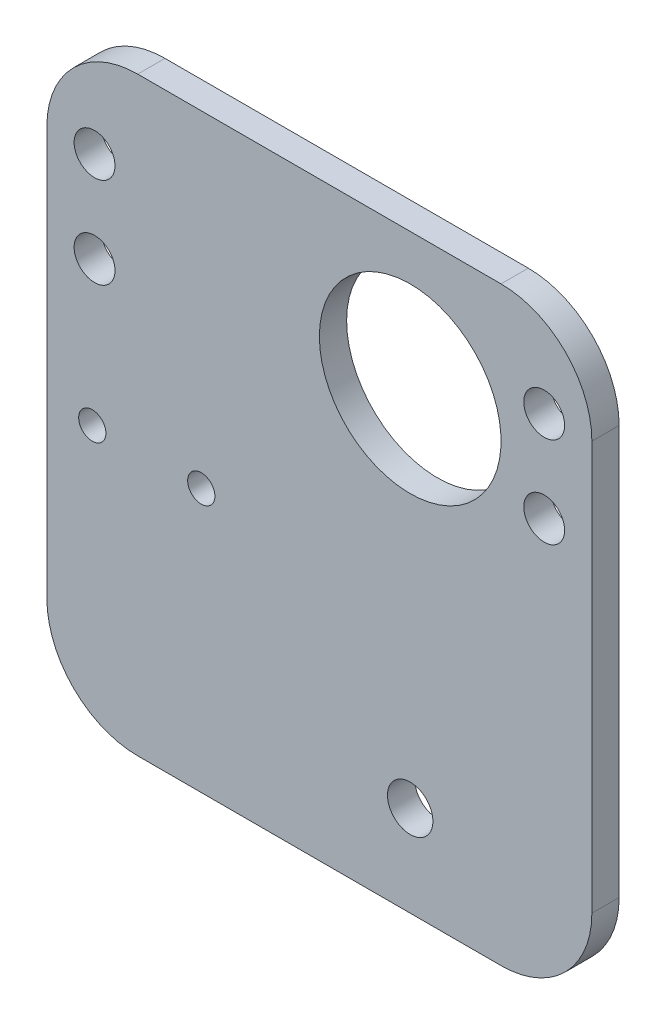
SolidWorks part; units mm, degrees
ref_plane "前视基准面" through (0, 0, 0) normal (0, 0, 1) x (1, 0, 0)
ref_plane "上视基准面" through (0, 0, 0) normal (0, 1, 0) x (1, 0, 0)
ref_plane "右视基准面" through (0, 0, 0) normal (1, 0, 0) x (0, 0, -1)
sketch "草图3" plane through (0, 0, 0) normal (0, 0, 1) x (1, 0, 0)
  line L0 (60.2665, 6.5325) -> (60.2665, 16.5325)
  line L1 (10.7665, 16.5325) -> (10.7665, 6.5325)
  line L2 (10.7665, 16.5325) -> (60.2665, 16.5325)
  circle A0 centre (60.2665, 16.5325) radius 3
  circle A1 centre (60.2665, 6.5325) radius 3
  circle A6 centre (10.7665, 6.5325) radius 3
  circle A7 centre (10.7665, 16.5325) radius 3
  dimension "D1" = 6
  dimension "D2" = 6
  dimension "D4" = 6
  dimension "D5" = 6
  dimension "D3" = 10
  dimension "D6" = 49.5
  dimension "D7" = 49.5
  dimension "D8" = 10
extrude "凸台-拉伸6" add sketch "草图3" along normal blind 0.001 contours A6 | A0 | A1 | A7
sketch "草图11" plane through (0, 0, 0.001) normal (0, 0, 1) x (1, 0, 0)
  circle A0 centre (10.7665, 16.5325) radius 2.25
  circle A1 centre (10.7665, 6.5325) radius 2.25
  circle A2 centre (60.2665, 16.5325) radius 2.25
  circle A3 centre (60.2665, 6.5325) radius 2.25
  dimension "D1" = 4.5
  dimension "D2" = 4.5
  dimension "D3" = 4.5
  dimension "D4" = 4.5
extrude "切除-拉伸2" cut sketch "草图11" against normal through all both and the other way through all
sketch "草图12" plane through (0, 0, 0.001) normal (0, 0, 1) x (1, 0, 0)
  line L4 (10.7665, 16.5325) -> (60.2665, 6.5325) construction
  line L5 (10.7665, 6.5325) -> (60.2665, 16.5325) construction
  line L6 (60.2665, 16.5325) -> (60.2665, 6.5325) construction
  line L7 (5.5165, 26.5325) -> (65.5165, 26.5325)
  line L8 (5.5165, 26.5325) -> (5.5165, 1.5325)
  line L9 (5.5165, -38.4675) -> (65.5165, -38.4675)
  line L10 (65.5165, 26.5325) -> (65.5165, -38.4675)
  line L11 (5.5165, 1.5325) -> (5.5165, -38.4675) construction
  line L13 (5.5165, -38.4675) -> (5.5165, 1.5325) construction
  line L16 (5.5165, 1.5325) -> (5.5165, -38.4675)
  circle A4 centre (45.5165, 11.5325) radius 10
  point P8 (35.5165, 11.5325)
  point P9 (35.5165, 26.5325)
  point P10 (-46.6091, 14.6442)
  point P11 (60.2665, 11.5325)
  dimension "D5" = 20
  dimension "D1" = 60
  dimension "D2" = 65
  dimension "D3" = 15
  dimension "D4" = 14.75
extrude "凸台-拉伸7" add sketch "草图12" along normal blind 3 contours L7 L10 L9 L16 L8
sketch "草图14" plane through (0, 0, 0.001) normal (0, 0, -1) x (-1, 0, 0)
  line L0 (-60.2665, 16.5325) -> (-60.2665, 6.5325) construction
  circle A0 centre (-60.2665, 6.5325) radius 2.25 construction
  circle A1 centre (-60.2665, 6.5325) radius 2.25
  circle A2 centre (-60.2665, 16.5325) radius 2.25 construction
  circle A3 centre (-60.2665, 16.5325) radius 2.25
  circle A4 centre (-10.7665, 6.5325) radius 2.25 construction
  circle A5 centre (-10.7665, 16.5325) radius 2.25 construction
  circle A6 centre (-10.7665, 6.5325) radius 2.25
  circle A7 centre (-10.7665, 16.5325) radius 2.25
  circle A8 centre (-45.5165, 11.5325) radius 10
  point P14 (-60.2665, 11.5325)
  point P15 (0.1696, -0.033)
  dimension "D2" = 20
  dimension "D1" = 14.75
extrude "切除-拉伸3" cut sketch "草图14" against normal blind 3
sketch "草图15" plane through (0, 0, 0.001) normal (0, 0, -1) x (-1, 0, 0)
  circle A0 centre (-45.5165, 11.5325) radius 10 construction
  circle A1 centre (-45.5165, 11.5325) radius 10
  circle A2 centre (-45.5165, -28.4675) radius 2.5
  dimension "D2" = 5
  dimension "D1" = 40
extrude "切除-拉伸4" cut sketch "草图15" against normal blind 3
sketch "草图16" plane through (0, 0, 3.001) normal (0, 0, 1) x (1, 0, 0)
  line L6 (5.5165, 26.5325) -> (5.5165, -38.4675) construction
  line L7 (5.5165, -38.4675) -> (65.5165, -38.4675) construction
  circle A0 centre (10.5165, -9.4675) radius 1.5
  circle A1 centre (22.5165, -9.4675) radius 1.5
  dimension "D1" = 3
  dimension "D2" = 5
  dimension "D3" = 29
  dimension "D5" = 12
  dimension "D4" = 2
extrude "切除-拉伸5" cut sketch "草图16" against normal blind 10
sketch "草图17" plane through (0, 0, 3.001) normal (0, 0, 1) x (1, 0, 0)
  circle A0 centre (45.5165, -28.4675) radius 9.5
  circle A1 centre (45.5165, -28.4675) radius 7.5
  dimension "D1" = 19
  dimension "D2" = 2
extrude "凸台-拉伸8" add sketch "草图17" against normal blind 4.9
fillet "圆角1" radius 10 4 edges at (65.5165, 26.5325, 1.501) (65.5165, -38.4675, 1.501) (5.5165, -38.4675, 1.501) (5.5165, 26.5325, 1.501)
